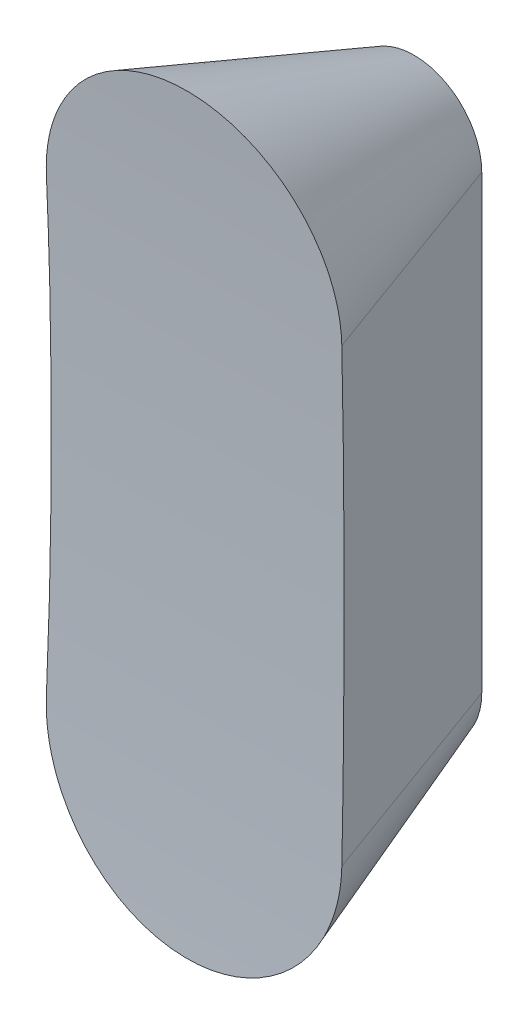
SolidWorks part; units mm, degrees
ref_plane "Plano frontal" through (0, 0, 0) normal (0, 0, 1) x (1, 0, 0)
ref_plane "Plano superior" through (0, 0, 0) normal (0, 1, 0) x (1, 0, 0)
ref_plane "Plano direito" through (0, 0, 0) normal (1, 0, 0) x (0, 0, -1)
sketch "Esboço1" plane through (0, 0, 0) normal (0, 0, 1) x (1, 0, 0)
  line L0 (0, 0) -> (0, 386.7762) construction
  line L1 (0, 0) -> (131.8833, 0) construction
  line L2 (75, -250) -> (75, 250)
  line L3 (-75, -250) -> (-75, 250)
  arc A0 (75, 250) -> (-75, 250) centre (0, 250) ccw
  arc A1 (75, -250) -> (-75, -250) centre (0, -250) cw
  point P11 (75, 0)
  point P13 (-75, 0)
  dimension "D1" = 75
  dimension "D2" = 250
extrude "Ressalto-extrusão1" add sketch "Esboço1" along normal blind 300 draft 20 draft outward yes
sketch "Esboço4" plane through (0, 0, 0) normal (1, 0, 0) x (0, 0, -1)
  line L0 (-300, 0) -> (-278.7137, 0) construction
  line L1 (-300, -250) -> (-300, 250) construction
  line L2 (-329.9333, 603.5714) -> (-300, 803.5714)
  line L3 (-300, 803.5714) -> (-270.0667, 603.5714)
  ellipse E0 centre (-300, 0) end of major axis (-300, -696.4286) minor radius 60 (-329.9333, 603.5714) -> (-270.0667, 603.5714) ccw
  dimension "D1" = 200
  dimension "D2" = 1500
  dimension "D3" = 120
extrude "Corte-extrusão1" cut sketch "Esboço4" against normal through all both and the other way through all
sketch "Esboço5" plane through (0, 0, 0) normal (1, 0, 0) x (0, 0, -1)
  line L0 (0, -190) -> (40, -190)
  line L1 (0, -250) -> (0, 250) construction
  line L2 (40, -190) -> (40, -230)
  line L3 (40, -230) -> (20, -230)
  line L4 (20, -230) -> (20, -210)
  line L5 (20, -210) -> (0, -210)
  line L6 (0, -210) -> (0, -190)
  line L7 (0, 0) -> (365.0997, 0) construction
  line L8 (40, 230) -> (20, 230)
  line L9 (40, 190) -> (40, 230)
  line L10 (0, 190) -> (40, 190)
  line L11 (0, 210) -> (0, 190)
  line L12 (20, 210) -> (0, 210)
  line L13 (20, 230) -> (20, 210)
  dimension "D1" = 20
  dimension "D2" = 40
  dimension "D3" = 20
  dimension "D4" = 20
  dimension "D5" = 210
